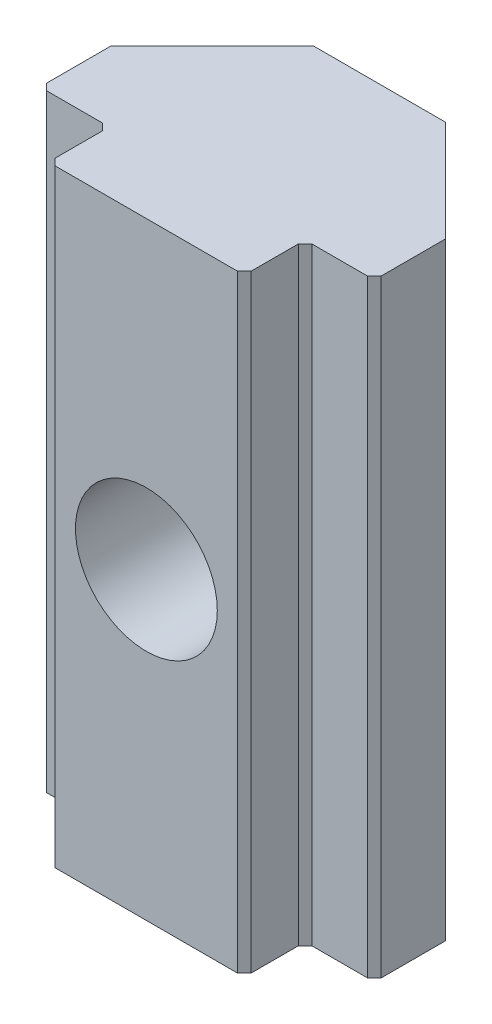
SolidWorks part; units mm, degrees
material "201 退火不锈钢 (SS)"
ref_plane "前视基准面" through (0, 0, 0) normal (0, 0, 1) x (1, 0, 0)
ref_plane "上视基准面" through (0, 0, 0) normal (0, 1, 0) x (1, 0, 0)
ref_plane "右视基准面" through (0, 0, 0) normal (1, 0, 0) x (0, 0, -1)
sketch "草图1" plane through (0, 0, 0) normal (0, 1, 0) x (1, 0, 0)
  line L0 (2.9, -2.55) -> (4.95, -2.55)
  line L1 (-4.95, -2.55) -> (-2.9, -2.55)
  line L2 (-4.95, -2.55) -> (-4.95, 2.55)
  line L3 (-4.95, 2.55) -> (4.95, 2.55)
  line L4 (4.95, -2.55) -> (4.95, 2.55)
  line L5 (-4.95, -2.55) -> (4.95, 2.55) construction
  line L6 (-4.95, 2.55) -> (4.95, -2.55) construction
  line L7 (-2.9, -4.35) -> (2.9, -4.35)
  line L8 (-2.9, -4.35) -> (-2.9, -2.55)
  line L10 (2.9, -4.35) -> (2.9, -2.55)
  line L11 (-2.9, -4.35) -> (2.9, -2.55) construction
  line L12 (-2.9, -2.55) -> (2.9, -4.35) construction
  point P0 (0, 0)
  point P6 (0, -3.45)
  dimension "D1" = 5.8
  dimension "D2" = 1.8
  dimension "D3" = 6.9
  dimension "D4" = 9.9
  dimension "D5" = 0
extrude "凸台-拉伸1" add sketch "草图1" along normal blind 18
chamfer "倒角1" distance 3 angle 45 2 edges at (-4.95, 9, -2.55) (4.95, 9, -2.55)
chamfer "倒角2" distance 0.2 angle 45 6 edges at (-2.9, 9, 2.55) (-4.95, 9, 2.55) (4.95, 9, 2.55) (2.9, 9, 2.55) (2.9, 9, 4.35) (-2.9, 9, 4.35)
hole_wizard "M5 螺纹孔1" positions "草图2" profile "草图3" tap size "M5" standard "GB" end condition through all
sketch "草图2" plane through (0, 0, 4.35) normal (0, 0, 1) x (1, 0, 0)
  point P0 (0, 9)
sketch "草图3" plane through (0, 9, 4.35) normal (1, 0, 0) x (0, -1, 0)
  line L0 (0, 0) -> (0, 6.9)
  line L1 (0, 6.9) -> (2.1, 6.9)
  line L2 (2.1, 6.9) -> (2.1, 0)
  line L5 (2.1, 0) -> (0, 0)
  line L11 (0, -6.35) -> (0, 107.95) construction
  dimension "通孔螺纹孔钻头直径" = 4.2
  dimension "通孔螺纹孔钻头深度" = 6.9
cosmetic thread "孔螺蚊线1" parameters "D2"=5
